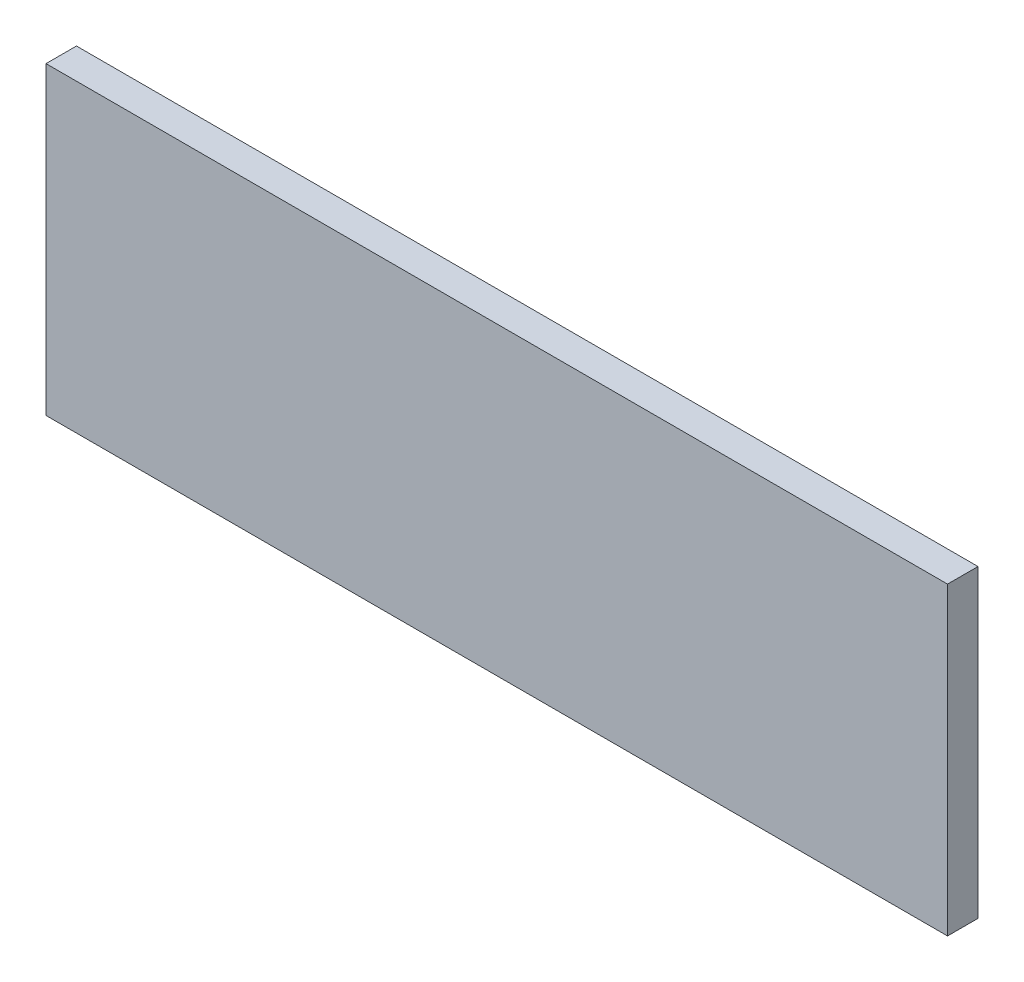
SolidWorks part; units mm, degrees
ref_plane "Plan de face" through (0, 0, 0) normal (0, 0, 1) x (1, 0, 0)
ref_plane "Plan de dessus" through (0, 0, 0) normal (0, 1, 0) x (1, 0, 0)
ref_plane "Plan de droite" through (0, 0, 0) normal (1, 0, 0) x (0, 0, -1)
sketch "Esquisse1" plane through (0, 0, 0) normal (0, 0, 1) x (1, 0, 0)
  line L1 (0, 0) -> (88.75, 0)
  line L2 (0, 0) -> (0, -30)
  line L3 (0, -30) -> (88.75, -30)
  line L4 (88.75, 0) -> (88.75, -30)
  dimension "D1" = 30
  dimension "D2" = 88.75
extrude "Boss.-Extru.1" add sketch "Esquisse1" along normal blind 3
